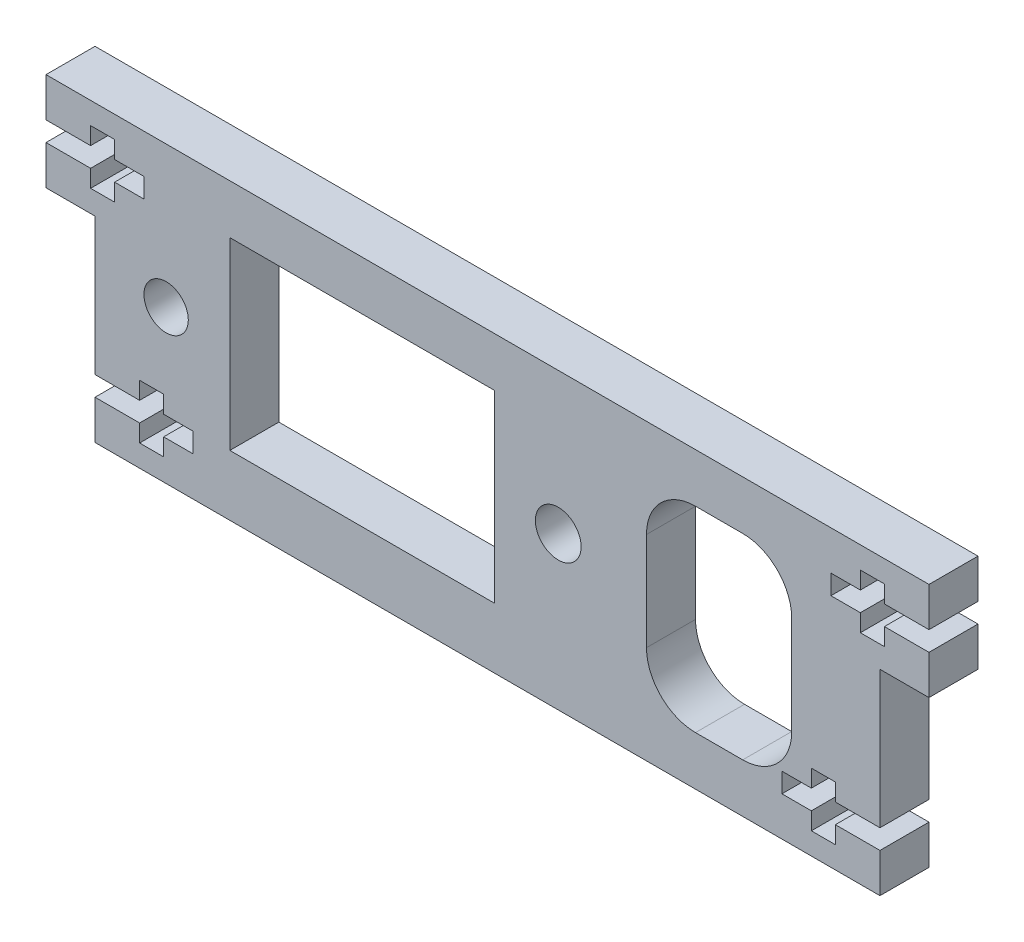
SolidWorks part; units mm, degrees
material "Acrílico (médio-alto impacto)"
ref_plane "Plano frontal" through (0, 0, 0) normal (0, 0, 1) x (1, 0, 0)
ref_plane "Plano superior" through (0, 0, 0) normal (0, 1, 0) x (1, 0, 0)
ref_plane "Plano direito" through (0, 0, 0) normal (1, 0, 0) x (0, 0, -1)
sketch "Esboço1" plane through (0, 0, 0) normal (0, 0, 1) x (1, 0, 0)
  line L0 (-26.7278, -21.587) -> (-26.7278, -1.587)
  line L1 (-26.7278, -1.587) -> (-31.7278, -1.587)
  line L2 (-31.7278, -1.587) -> (-31.7278, 8.413)
  line L3 (-31.7278, 8.413) -> (58.3422, 8.413)
  line L4 (58.3422, 8.413) -> (58.3422, -1.587)
  line L5 (58.3422, -1.587) -> (53.3422, -1.587)
  line L6 (53.3422, -1.587) -> (53.3422, -21.587)
  line L7 (-26.7278, -21.587) -> (53.3422, -21.587)
  dimension "D1" = 20
  dimension "D2" = 5
  dimension "D3" = 10
  dimension "D4" = 90.07
  dimension "D5" = 10
  dimension "D6" = 5
  dimension "D7" = 20
extrude "Ressalto-extrusão1" add sketch "Esboço1" along normal blind 5
sketch "Esboço2" plane through (0, 0, 5) normal (0, 0, 1) x (1, 0, 0)
  line L0 (-31.7278, 8.413) -> (-31.7278, -1.587) construction
  line L1 (-31.7278, 2.413) -> (-27.1778, 2.413)
  line L2 (-31.7278, 2.413) -> (-31.7278, 4.413)
  line L3 (-31.7278, 4.413) -> (-27.1778, 4.413)
  line L4 (-21.7278, 2.413) -> (-21.7278, 4.413)
  line L5 (58.3422, 8.413) -> (-31.7278, 8.413) construction
  line L6 (-27.1778, 0.643) -> (-24.7278, 0.643)
  line L7 (-27.1778, 0.643) -> (-27.1778, 2.413)
  line L8 (-27.1778, 6.183) -> (-24.7278, 6.183)
  line L9 (-24.7278, 0.643) -> (-24.7278, 2.413)
  line L12 (-27.1778, 4.413) -> (-27.1778, 6.183)
  line L13 (-24.7278, 4.413) -> (-24.7278, 6.183)
  line L14 (-24.7278, 2.413) -> (-21.7278, 2.413)
  line L15 (-24.7278, 4.413) -> (-21.7278, 4.413)
  line L16 (13.3072, -21.587) -> (13.3072, -15.1258) construction
  line L18 (51.3422, 4.413) -> (48.3422, 4.413)
  line L19 (51.3422, 2.413) -> (48.3422, 2.413)
  line L20 (51.3422, 4.413) -> (51.3422, 6.183)
  line L21 (53.7922, 4.413) -> (53.7922, 6.183)
  line L22 (51.3422, 0.643) -> (51.3422, 2.413)
  line L23 (53.7922, 6.183) -> (51.3422, 6.183)
  line L24 (53.7922, 0.643) -> (53.7922, 2.413)
  line L25 (53.7922, 0.643) -> (51.3422, 0.643)
  line L26 (48.3422, 2.413) -> (48.3422, 4.413)
  line L27 (58.3422, 4.413) -> (53.7922, 4.413)
  line L28 (58.3422, 2.413) -> (58.3422, 4.413)
  line L29 (58.3422, 2.413) -> (53.7922, 2.413)
  line L30 (-26.7278, -1.587) -> (-26.7278, -21.587) construction
  line L31 (-26.7278, -17.587) -> (-22.1778, -17.587)
  line L32 (-26.7278, -17.587) -> (-26.7278, -15.587)
  line L33 (-26.7278, -15.587) -> (-22.1778, -15.587)
  line L34 (-16.7278, -17.587) -> (-16.7278, -15.587)
  line L35 (-22.1778, -15.587) -> (-22.1778, -13.817)
  line L36 (-22.1778, -19.357) -> (-19.7278, -19.357)
  line L37 (-22.1778, -19.357) -> (-22.1778, -17.587)
  line L38 (-22.1778, -13.817) -> (-19.7278, -13.817)
  line L39 (-19.7278, -19.357) -> (-19.7278, -17.587)
  line L40 (-19.7278, -15.587) -> (-19.7278, -13.817)
  line L41 (-19.7278, -17.587) -> (-16.7278, -17.587)
  line L42 (-19.7278, -15.587) -> (-16.7278, -15.587)
  line L43 (46.3422, -15.587) -> (43.3422, -15.587)
  line L44 (46.3422, -17.587) -> (43.3422, -17.587)
  line L45 (46.3422, -15.587) -> (46.3422, -13.817)
  line L46 (46.3422, -19.357) -> (46.3422, -17.587)
  line L47 (48.7922, -13.817) -> (46.3422, -13.817)
  line L48 (48.7922, -19.357) -> (48.7922, -17.587)
  line L49 (48.7922, -19.357) -> (46.3422, -19.357)
  line L50 (48.7922, -15.587) -> (48.7922, -13.817)
  line L51 (43.3422, -17.587) -> (43.3422, -15.587)
  line L52 (53.3422, -15.587) -> (48.7922, -15.587)
  line L53 (53.3422, -17.587) -> (53.3422, -15.587)
  line L54 (53.3422, -17.587) -> (48.7922, -17.587)
  dimension "D1" = 10
  dimension "D2" = 2
  dimension "D3" = 1.77
  dimension "D4" = 1.77
  dimension "D5" = 2.45
  dimension "D6" = 4.55
  dimension "D7" = 2.23
  dimension "D8" = 1.77
  dimension "D9" = 1.77
  dimension "D10" = 10
  dimension "D11" = 4.55
  dimension "D12" = 2.45
  dimension "D13" = 2
  dimension "D14" = 18
extrude "Corte-extrusão1" cut sketch "Esboço2" against normal through all
sketch "Esboço3" plane through (0, 0, 5) normal (0, 0, 1) x (1, 0, 0)
  line L0 (58.3422, 8.413) -> (-31.7278, 8.413) construction
  line L1 (-12.9748, 3.3897) -> (14.0252, 3.3897)
  line L2 (-12.9748, 3.3897) -> (-12.9748, -15.4103)
  line L3 (-12.9748, -15.4103) -> (14.0252, -15.4103)
  line L4 (14.0252, 3.3897) -> (14.0252, -15.4103)
  line L5 (34.5252, 3.413) -> (39.3422, 3.413)
  line L6 (29.5252, -1.587) -> (29.5252, -11.587)
  line L7 (34.5252, -16.587) -> (39.3422, -16.587)
  line L8 (44.3422, -1.587) -> (44.3422, -11.587)
  line L9 (-26.7278, -21.587) -> (53.3422, -21.587) construction
  line L10 (53.3422, -21.587) -> (53.3422, -17.587) construction
  circle A0 centre (-19.4748, -6.0103) radius 2.2627
  circle A1 centre (20.5252, -6.0103) radius 2.3327
  arc A2 (34.5252, 3.413) -> (29.5252, -1.587) centre (34.5252, -1.587) ccw
  arc A3 (39.3422, 3.413) -> (44.3422, -1.587) centre (39.3422, -1.587) cw
  arc A4 (39.3422, -16.587) -> (44.3422, -11.587) centre (39.3422, -11.587) ccw
  arc A5 (29.5252, -11.587) -> (34.5252, -16.587) centre (34.5252, -11.587) ccw
  point P18 (53.3422, -19.587)
  dimension "D1" = 40
  dimension "D6" = 9.4
  dimension "D11" = 5
  dimension "D2" = 6.5
  dimension "D3" = 6.5
  dimension "D4" = 27
  dimension "D5" = 18.8
  dimension "D7" = 5
  dimension "D8" = 5
  dimension "D9" = 9
  dimension "D10" = 9
extrude "Corte-extrusão2" cut sketch "Esboço3" against normal through all
